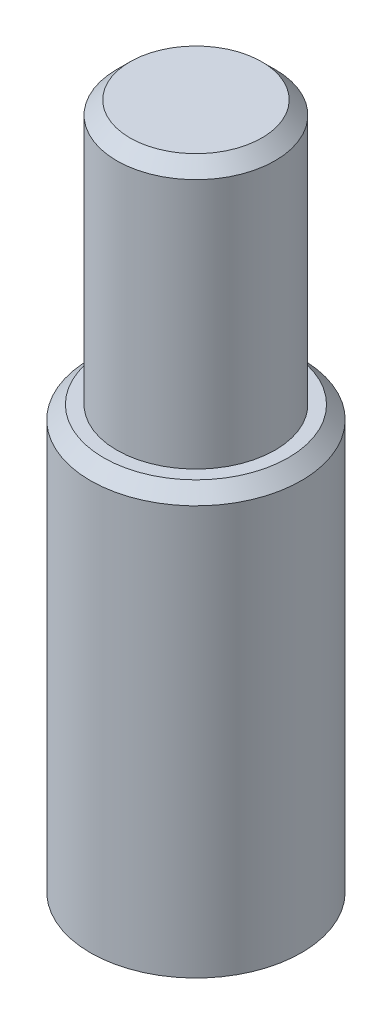
SolidWorks part; units mm, degrees
ref_plane "Ebene vorne" through (0, 0, 0) normal (0, 0, 1) x (1, 0, 0)
ref_plane "Ebene oben" through (0, 0, 0) normal (0, 1, 0) x (1, 0, 0)
ref_plane "Ebene rechts" through (0, 0, 0) normal (1, 0, 0) x (0, 0, -1)
sketch "Skizze1" plane through (0, 0, 0) normal (0, 0, 1) x (1, 0, 0)
  line L0 (0, 66.9239) -> (0, -67.1803) construction
  line L1 (0, 0) -> (-8, 0)
  line L2 (-8, 0) -> (-8, 32)
  line L3 (-8, 32) -> (-6, 32)
  line L4 (-6, 32) -> (-6, 52)
  line L5 (-6, 52) -> (0, 52)
  line L6 (0, 52) -> (0, 0)
  dimension "D1" = 52
  dimension "D2" = 12
  dimension "D3" = 16
  dimension "D4" = 32
revolve "Rotation1" add sketch "Skizze1" angle 360 about L0
hole_wizard "M8 Gewindebohrung1" positions "Skizze3" profile "Skizze2" tap size "M8" standard "DIN"
sketch "Skizze3" plane through (0, 0, 0) normal (0, -1, 0) x (-1, 0, 0)
  point P0 (0, 0)
sketch "Skizze2" plane through (0, 0, 0) normal (1, 0, 0) x (0, 0, -1)
  line L0 (0, 0) -> (0, 17.0429)
  line L1 (0, 17.0429) -> (3.4, 15)
  line L2 (3.4, 15) -> (3.4, 0)
  line L5 (3.4, 0) -> (0, 0)
  line L10 (0, 17.0429) -> (-3.4, 15) construction
  line L11 (0, -6.35) -> (0, 107.95) construction
  dimension "Bohrerdurchmesser" = 6.8
  dimension "Bohrungstiefe" = 15
  dimension "Spitzenwinkel" = 118
cosmetic thread "Bohrungsgewinde1" parameters "D1"=10, "D2"=8
chamfer "Fase1" distance 1 angle 45 1 edges at (0, 52, 6)
chamfer "Fase2" distance 1 angle 45 1 edges at (0, 32, 8)
